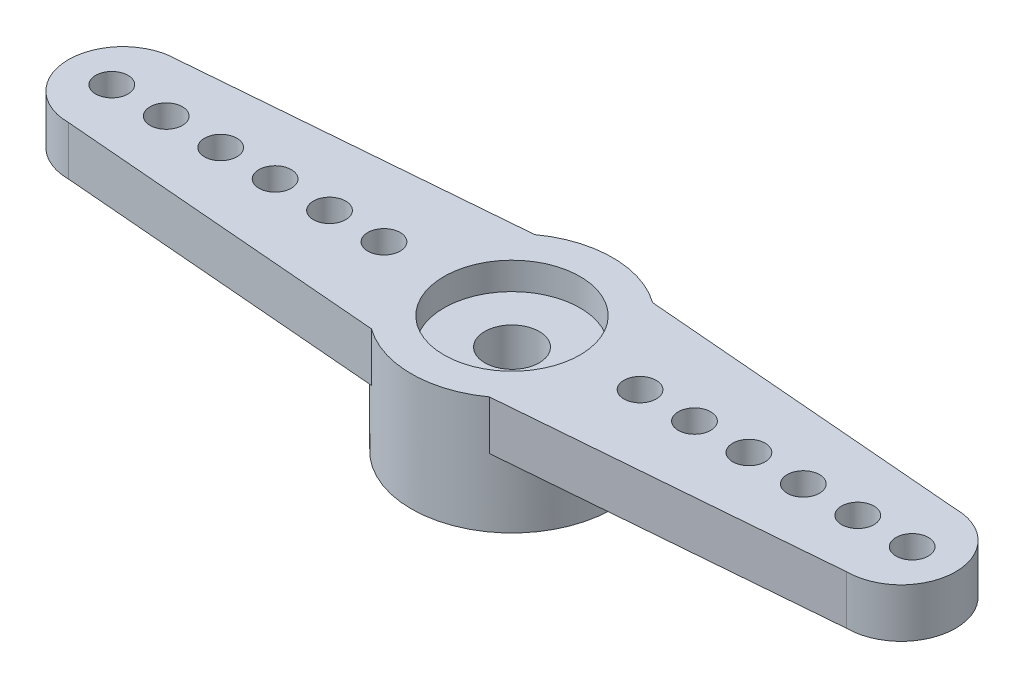
SolidWorks part; units mm, degrees
ref_plane "Alzado" through (0, 0, 0) normal (0, 0, 1) x (1, 0, 0)
ref_plane "Planta" through (0, 0, 0) normal (0, 1, 0) x (1, 0, 0)
ref_plane "Vista lateral" through (0, 0, 0) normal (1, 0, 0) x (0, 0, -1)
sketch "Croquis1" plane through (0, 0, 0) normal (0, 1, 0) x (1, 0, 0)
  circle A0 centre (0, 0) radius 3.7
  dimension "D1" = 7.4
extrude "Saliente-Extruir2" add sketch "Croquis1" along normal blind 4.3 contours A0
sketch "Croquis2" plane through (0, 0, 0) normal (0, -1, 0) x (1, 0, 0)
  circle A0 centre (0, 0) radius 2.5
  dimension "D1" = 5
extrude "Cortar-Extruir1" cut sketch "Croquis2" against normal blind 1.5
sketch "Croquis3" plane through (0, 4.3, 0) normal (0, 1, 0) x (1, 0, 0)
  circle A0 centre (0, 0) radius 2.5
  dimension "D1" = 5
extrude "Cortar-Extruir2" cut sketch "Croquis3" against normal blind 1
sketch "Croquis4" plane through (0, 3.3, 0) normal (0, 1, 0) x (1, 0, 0)
  circle A0 centre (0, 0) radius 1
  dimension "D1" = 2
extrude "Cortar-Extruir3" cut sketch "Croquis4" against normal blind 1.8
sketch "Croquis5" plane through (0, 4.3, 0) normal (0, 1, 0) x (1, 0, 0)
  line L0 (0, 0) -> (-2.1656, 0) construction
  line L1 (-2.1656, 3) -> (-3.1202, 0)
  line L2 (-3.1202, 0) -> (-2.1656, -3)
  line L3 (-2.1656, 0) -> (-2.5, 0) construction
  line L4 (-3.7, 0) -> (-16.3, 0) construction
  line L5 (-14.3, 0) -> (-14.3, 2) construction
  line L6 (-14.3, 0) -> (-14.3, -2) construction
  line L7 (-2.1656, 3) -> (-14.3, 2)
  line L8 (-2.1656, -3) -> (-14.3, -2)
  line L9 (0, 5.1944) -> (0, -4.3435) construction
  line L10 (3.1202, 0) -> (2.1656, -3)
  line L11 (2.1656, -3) -> (14.3, -2)
  line L12 (2.1656, 3) -> (14.3, 2)
  line L13 (2.1656, 3) -> (3.1202, 0)
  arc A0 (-14.3, 2) -> (-14.3, -2) centre (-14.3, 0) ccw
  arc A1 (14.3, 2) -> (14.3, -2) centre (14.3, 0) cw
  circle A3 centre (0, 0) radius 3.7 construction
  circle A4 centre (0, 0) radius 2.5 construction
  point P2 (-14.3, 0)
  dimension "D1" = 2.1656
  dimension "D2" = 12.6
  dimension "D3" = 2
  dimension "D4" = 2
  dimension "D5" = 2
extrude "Saliente-Extruir3" add sketch "Croquis5" against normal blind 1.8
sketch "Croquis6" plane through (0, 4.3, 0) normal (0, 1, 0) x (1, 0, 0)
  line L0 (0, 0) -> (-16.3, 0) construction
  line L1 (2, 0) -> (-14.3, 0) construction
  line L2 (4, 0) -> (-12.3, 0) construction
  line L3 (6, 0) -> (-10.3, 0) construction
  line L4 (8, 0) -> (-8.3, 0) construction
  line L5 (10, 0) -> (-6.3, 0) construction
  line L6 (0, 5.4913) -> (0, -4.5375) construction
  arc A0 (-14.3, 2) -> (-14.3, -2) centre (-14.3, 0) ccw construction
  circle A1 centre (-14.705, 0) radius 0.595
  circle A2 centre (-12.705, 0) radius 0.595
  circle A3 centre (-10.705, 0) radius 0.595
  circle A4 centre (-8.705, 0) radius 0.595
  circle A5 centre (-6.705, 0) radius 0.595
  circle A6 centre (-4.705, 0) radius 0.595
  circle A7 centre (14.705, 0) radius 0.595
  circle A8 centre (12.705, 0) radius 0.595
  circle A9 centre (10.705, 0) radius 0.595
  circle A10 centre (8.705, 0) radius 0.595
  circle A11 centre (6.705, 0) radius 0.595
  circle A12 centre (4.705, 0) radius 0.595
  point P6 (-14.705, 0)
  dimension "D2" = 1.19
  dimension "D1" = 1.595
  dimension "D3" = 6
extrude "Cortar-Extruir4" cut sketch "Croquis6" against normal blind 1.8
